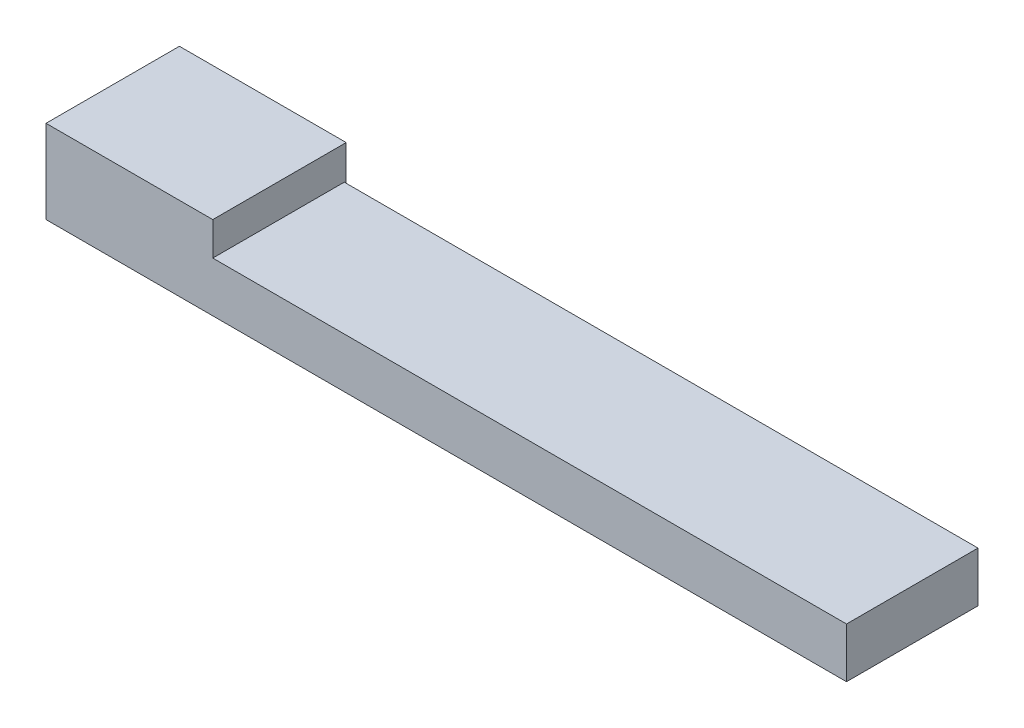
SolidWorks part; units mm, degrees
ref_plane "Front Plane" through (0, 0, 0) normal (0, 0, 1) x (1, 0, 0)
ref_plane "Top Plane" through (0, 0, 0) normal (0, 1, 0) x (1, 0, 0)
ref_plane "Right Plane" through (0, 0, 0) normal (1, 0, 0) x (0, 0, -1)
sketch "Sketch1" plane through (0, 0, 0) normal (0, 1, 0) x (1, 0, 0)
  line L1 (-62.2244, 2375.5899) -> (2985.7756, 2375.5899)
  line L2 (-62.2244, 2375.5899) -> (-62.2244, -62.8101)
  line L3 (-62.2244, -62.8101) -> (2985.7756, -62.8101)
  line L4 (2985.7756, 2375.5899) -> (2985.7756, -62.8101)
  dimension "D1" = 2438.4
  dimension "D2" = 3048
extrude "Boss-Extrude1" add sketch "Sketch1" along normal blind 1524
sketch "Sketch3" plane through (0, 0, 0) normal (0, -1, 0) x (1, 0, 0)
  line L0 (2985.7756, 62.8101) -> (2985.7756, -2375.5899) construction
  line L1 (2985.7756, 62.8101) -> (14568.1756, 62.8101)
  line L2 (2985.7756, 62.8101) -> (2985.7756, -2340.2818)
  line L3 (2985.7756, -2340.2818) -> (14568.1756, -2340.2818)
  line L4 (14568.1756, 62.8101) -> (14568.1756, -2340.2818)
  dimension "D1" = 11582.4
extrude "Boss-Extrude2" add sketch "Sketch3" against normal blind 914.4
